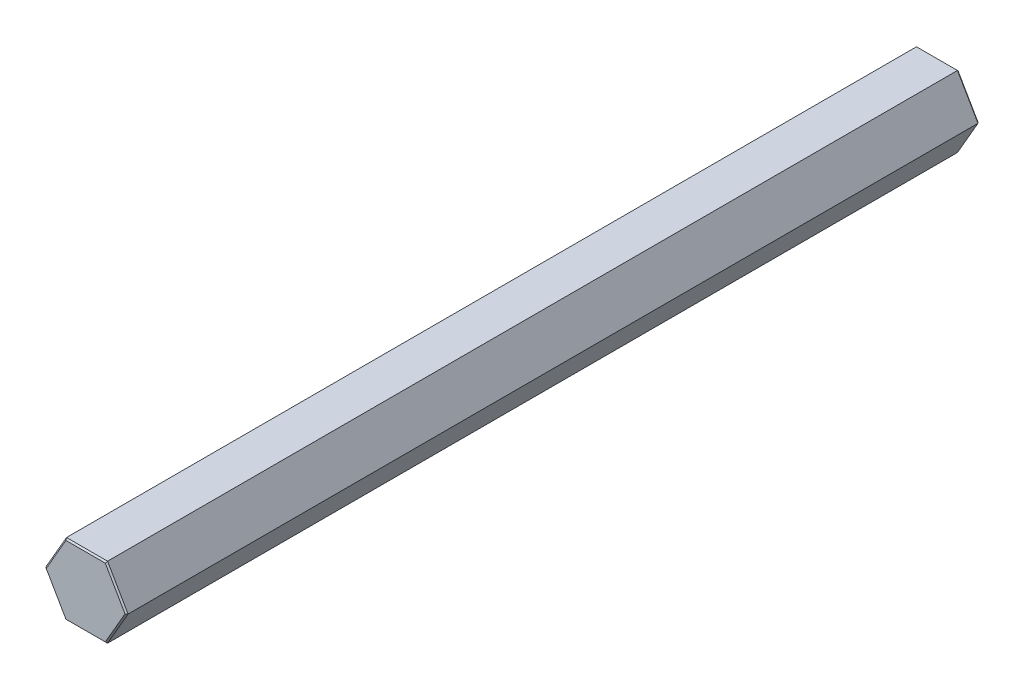
SolidWorks part; units mm, degrees
material "1060 Alloy"
ref_plane "Front Plane" through (0, 0, 0) normal (0, 0, 1) x (1, 0, 0)
ref_plane "Top Plane" through (0, 0, 0) normal (0, 1, 0) x (1, 0, 0)
ref_plane "Right Plane" through (0, 0, 0) normal (1, 0, 0) x (0, 0, -1)
ref_plane "Plane1" through (0, 0, 0) normal (0, 0, -1) x (-1, 0, 0)
sketch "Sketch1" plane through (0, 0, 0) normal (0, 0, -1) x (-1, 0, 0)
  line L0 (3.6662, 6.35) -> (-3.6662, 6.35)
  line L1 (-3.6662, 6.35) -> (-7.3323, 0)
  line L2 (-7.3323, 0) -> (-3.6662, -6.35)
  line L3 (-3.6662, -6.35) -> (3.6662, -6.35)
  line L4 (3.6662, -6.35) -> (7.3323, 0)
  line L5 (7.3323, 0) -> (3.6662, 6.35)
extrude "Boss-Extrude1" add sketch "Sketch1" against normal blind 152.4
chamfer "Chamfer1" distance 0.254 angle 45 12 edges at (0, -6.35, 0) (5.4993, -3.175, 0) (-5.4993, -3.175, 0) (5.4993, 3.175, 0) (-5.4993, 3.175, 0) (0, 6.35, 0) (-5.4993, -3.175, 152.4) (0, -6.35, 152.4) (-5.4993, 3.175, 152.4) (5.4993, -3.175, 152.4) (0, 6.35, 152.4) (5.4993, 3.175, 152.4)
